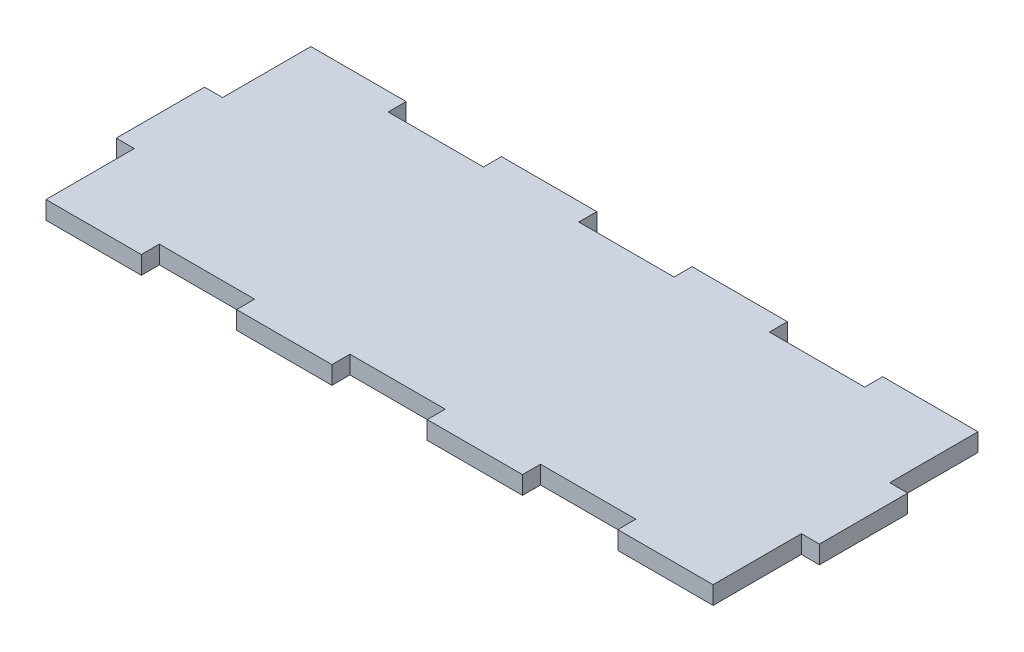
SolidWorks part; units mm, degrees
ref_plane "Front Plane" through (0, 0, 0) normal (0, 0, 1) x (1, 0, 0)
ref_plane "Top Plane" through (0, 0, 0) normal (0, 1, 0) x (1, 0, 0)
ref_plane "Right Plane" through (0, 0, 0) normal (1, 0, 0) x (0, 0, -1)
sketch "Sketch1" plane through (0, 0, 0) normal (0, 1, 0) x (1, 0, 0)
  line L1 (0, 0) -> (68.5, 0)
  line L2 (0, 0) -> (0, 23.5)
  line L3 (0, 23.5) -> (68.5, 23.5)
  line L4 (68.5, 0) -> (68.5, 23.5)
  dimension "D1" = 23.5
  dimension "D2" = 68.5
extrude "Boss-Extrude1" add sketch "Sketch1" along normal blind 1.85
sketch "Sketch2" plane through (0, 1.85, 0) normal (0, 1, 0) x (1, 0, 0)
  line L0 (9.7857, -1.85) -> (19.5714, -1.85) construction
  line L1 (0, 0) -> (9.7857, 0)
  line L2 (0, 0) -> (0, -1.85)
  line L3 (0, -1.85) -> (9.7857, -1.85)
  line L4 (9.7857, 0) -> (9.7857, -1.85)
  line L5 (19.5714, 0) -> (29.3571, 0)
  line L6 (19.5714, 0) -> (19.5714, -1.85)
  line L7 (19.5714, -1.85) -> (29.3571, -1.85)
  line L8 (29.3571, 0) -> (29.3571, -1.85)
  line L9 (29.3571, -1.85) -> (39.1429, -1.85) construction
  line L10 (39.1429, 0) -> (48.9286, 0)
  line L11 (39.1429, 0) -> (39.1429, -1.85)
  line L12 (39.1429, -1.85) -> (48.9286, -1.85)
  line L13 (48.9286, 0) -> (48.9286, -1.85)
  line L14 (48.9286, -1.85) -> (58.7143, -1.85) construction
  line L15 (58.7143, 0) -> (68.5, 0)
  line L16 (58.7143, 0) -> (58.7143, -1.85)
  line L17 (58.7143, -1.85) -> (68.5, -1.85)
  line L18 (68.5, 0) -> (68.5, -1.85)
  line L19 (68.5, -1.85) -> (78.2857, -1.85) construction
  line L20 (0, 11.75) -> (68.5, 11.75) construction
  line L21 (0, 23.5) -> (0, 0) construction
  line L22 (68.5, 0) -> (68.5, 23.5) construction
  line L23 (0, -1.85) -> (-1.85, -1.85) construction
  line L24 (-1.85, 7.2167) -> (-1.85, -1.85) construction
  line L25 (0, 16.2833) -> (-1.85, 16.2833)
  line L26 (0, 16.2833) -> (0, 7.2167)
  line L27 (0, 7.2167) -> (-1.85, 7.2167)
  line L28 (-1.85, 16.2833) -> (-1.85, 7.2167)
  line L29 (58.7143, 23.5) -> (58.7143, 25.35)
  line L30 (58.7143, 25.35) -> (68.5, 25.35)
  line L31 (68.5, 23.5) -> (68.5, 25.35)
  line L32 (58.7143, 23.5) -> (68.5, 23.5)
  line L33 (39.1429, 23.5) -> (39.1429, 25.35)
  line L34 (39.1429, 25.35) -> (48.9286, 25.35)
  line L35 (48.9286, 23.5) -> (48.9286, 25.35)
  line L36 (39.1429, 23.5) -> (48.9286, 23.5)
  line L37 (19.5714, 23.5) -> (19.5714, 25.35)
  line L38 (19.5714, 25.35) -> (29.3571, 25.35)
  line L39 (29.3571, 23.5) -> (29.3571, 25.35)
  line L40 (19.5714, 23.5) -> (29.3571, 23.5)
  line L41 (0, 25.35) -> (9.7857, 25.35)
  line L42 (9.7857, 23.5) -> (9.7857, 25.35)
  line L43 (0, 23.5) -> (9.7857, 23.5)
  line L44 (0, 23.5) -> (0, 25.35)
  line L45 (34.25, 0) -> (34.25, 23.5) construction
  line L46 (0, 0) -> (68.5, 0) construction
  line L47 (68.5, 23.5) -> (0, 23.5) construction
  line L48 (68.5, 7.2167) -> (70.35, 7.2167)
  line L49 (70.35, 16.2833) -> (70.35, 7.2167)
  line L50 (68.5, 16.2833) -> (70.35, 16.2833)
  line L51 (68.5, 16.2833) -> (68.5, 7.2167)
  point P31 (-1.85, 11.75)
  point P32 (-1.85, 11.75)
  dimension "D2" = 1.85
  dimension "D1" = 4
extrude "Boss-Extrude2" add sketch "Sketch2" against normal up to surface (1.85 mm away) up to face at (34.25, 0, -11.75)
equation "\"D1@Sketch1\"= 20 + \"thick\"*2"
equation "\"D1@Boss-Extrude1\"=\"thick\"+\"veneer_thickness\""
equation "\"D2@Sketch2\"=\"thick\"+\"veneer_thickness\""
equation "\"D2@Sketch1\"=65 + \"thick\"*2"
equation "\"veneer_thickness\"= 0.1mm"
equation "\"thick\"= 1.75mm"
